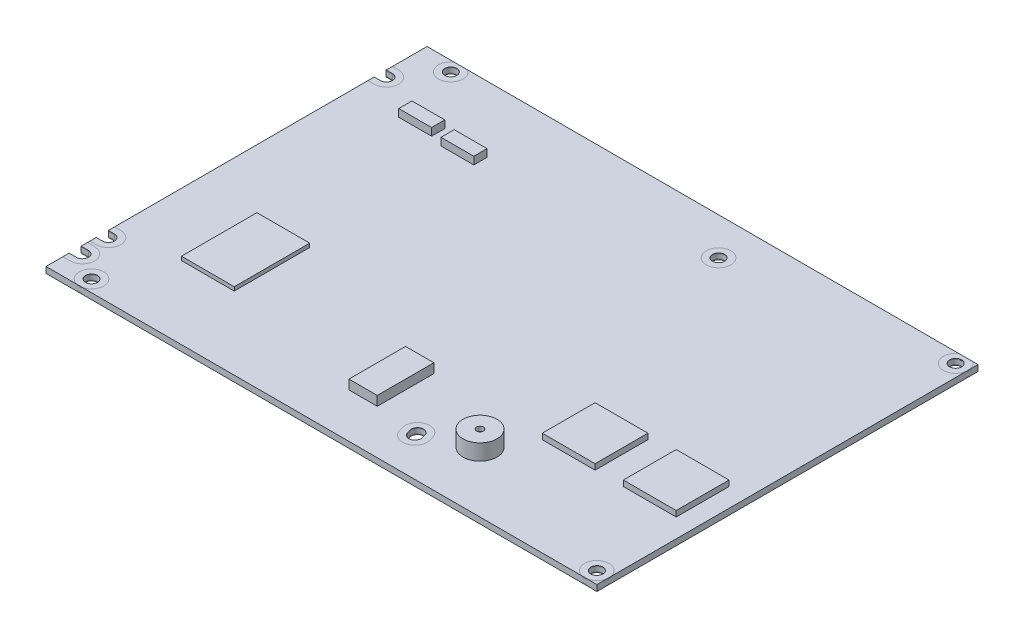
SolidWorks part; units mm, degrees
ref_plane "Alzado" through (0, 0, 0) normal (0, 0, 1) x (1, 0, 0)
ref_plane "Planta" through (0, 0, 0) normal (0, 1, 0) x (1, 0, 0)
ref_plane "Vista lateral" through (0, 0, 0) normal (1, 0, 0) x (0, 0, -1)
sketch "Croquis1" plane through (0, 0, 0) normal (0, 1, 0) x (1, 0, 0)
  line L0 (0, -14.02) -> (0, -84.48)
  line L1 (0, 0) -> (146.04, 0)
  line L2 (0, 0) -> (0, -10.82)
  line L3 (0, -101) -> (146.04, -101)
  line L4 (146.04, 0) -> (146.04, -101)
  line L5 (1.64, -10.82) -> (0, -10.82)
  line L6 (1.93, -91.68) -> (0, -91.68)
  line L7 (1.64, -14.02) -> (0, -14.02)
  line L8 (88.899, -89.4526) -> (89.169, -90.4026)
  line L9 (0, -94.88) -> (1.93, -94.88)
  line L10 (1.64, -84.48) -> (0, -84.48)
  line L11 (0, -94.88) -> (0, -101)
  line L12 (0, -87.68) -> (1.64, -87.68)
  line L13 (0, -87.68) -> (0, -91.68)
  line L14 (85.821, -90.3274) -> (86.091, -91.2774)
  circle A0 centre (8.99, -2.7) radius 1.6
  arc A1 (1.64, -14.02) -> (1.64, -10.82) centre (1.64, -12.42) ccw
  circle A2 centre (87.15, -9.88) radius 1.6
  circle A3 centre (142.8, -2.68) radius 1.6
  arc A4 (1.64, -87.68) -> (1.64, -84.48) centre (1.64, -86.08) ccw
  arc A5 (1.93, -94.88) -> (1.93, -91.68) centre (1.93, -93.28) ccw
  circle A6 centre (8.89, -97.82) radius 1.6
  circle A7 centre (142.8, -97.8) radius 1.6
  arc A8 (88.899, -89.4526) -> (85.821, -90.3274) centre (87.36, -89.89) ccw
  arc A9 (86.091, -91.2774) -> (89.169, -90.4026) centre (87.63, -90.84) ccw
  dimension "D3" = 3.2
  dimension "D6" = 3.2
  dimension "D10" = 3.2
  dimension "D13" = 3.2
  dimension "D16" = 3.2
  dimension "D17" = 3.2
  dimension "D22" = 3.2
  dimension "D25" = 3.2
  dimension "D28" = 3.2
  dimension "D29" = 3.2
  dimension "D1" = 146.04
  dimension "D2" = 101
  dimension "D4" = 8.99
  dimension "D5" = 2.7
  dimension "D7" = 1.64
  dimension "D8" = 12.42
  dimension "D9" = 3.2
  dimension "D11" = 87.15
  dimension "D12" = 9.88
  dimension "D14" = 2.68
  dimension "D15" = 142.8
  dimension "D18" = 1.93
  dimension "D19" = 1.64
  dimension "D20" = 86.08
  dimension "D21" = 93.28
  dimension "D23" = 8.89
  dimension "D24" = 97.82
  dimension "D26" = 142.8
  dimension "D27" = 97.8
  dimension "D30" = 87.36
  dimension "D31" = 87.63
  dimension "D32" = 89.89
  dimension "D33" = 90.84
extrude "Extruir1" add sketch "Croquis1" along normal blind 1.6
sketch "Croquis2" plane through (0, 1.6, 0) normal (0, 1, 0) x (1, 0, 0)
  line L0 (1.64, -9.17) -> (-2.3258, -9.17)
  line L1 (-2.3258, -9.17) -> (-2.3258, -15.67)
  line L2 (-2.3258, -15.67) -> (1.64, -15.67)
  line L3 (1.64, -82.83) -> (-3.1843, -82.83)
  line L4 (-3.1843, -82.83) -> (-3.1843, -89.33)
  line L5 (-3.1843, -89.33) -> (1.64, -89.33)
  line L6 (1.93, -90.03) -> (-3.1843, -90.03)
  line L7 (-3.1843, -90.03) -> (-3.1843, -96.53)
  line L8 (-3.1843, -96.53) -> (1.93, -96.53)
  line L9 (90.4862, -89.0015) -> (90.7562, -89.9515)
  line L10 (84.2338, -90.7785) -> (84.5038, -91.7285)
  circle A0 centre (8.99, -2.7) radius 3.25
  arc A1 (1.64, -15.67) -> (1.64, -9.17) centre (1.64, -12.42) ccw
  arc A2 (1.64, -89.33) -> (1.64, -82.83) centre (1.64, -86.08) ccw
  arc A3 (1.93, -96.53) -> (1.93, -90.03) centre (1.93, -93.28) ccw
  circle A4 centre (8.89, -97.82) radius 3.25
  circle A5 centre (87.15, -9.88) radius 3.25
  circle A6 centre (142.8, -2.68) radius 3.25
  circle A7 centre (142.8, -97.8) radius 3.25
  arc A8 (90.4862, -89.0015) -> (84.2338, -90.7785) centre (87.36, -89.89) ccw
  arc A9 (84.5038, -91.7285) -> (90.7562, -89.9515) centre (87.63, -90.84) ccw
  dimension "D1" = 6.5
  dimension "D2" = 6.5
  dimension "D3" = 6.5
  dimension "D4" = 6.5
  dimension "D5" = 6.5
  dimension "D6" = 6.5
  dimension "D7" = 6.5
  dimension "D8" = 6.5
  dimension "D9" = 6.5
  dimension "D10" = 6.5
extrude "Cortar-Extruir1" cut sketch "Croquis2" against normal blind 0.2
ref_plane "Plano1" through (0, 0.8, 0) normal (0, 1, 0) x (-1, 0, 0)
mirror "Simetría1" about plane through (0, 0.8, 0) normal (0, 1, 0) of "Cortar-Extruir1"
sketch "Croquis3" plane through (0, 1.4, 0) normal (0, 1, 0) x (1, 0, 0)
  line L0 (85.821, -90.3274) -> (86.091, -91.2774) construction
  line L1 (8.2191, -101) -> (9.5609, -101)
  line L2 (8.2191, -101) -> (9.5609, -101)
  line L3 (89.169, -90.4026) -> (88.899, -89.4526) construction
  line L4 (84.2338, -90.7785) -> (84.5038, -91.7285)
  line L5 (90.7562, -89.9515) -> (90.4862, -89.0015)
  line L6 (0, -90.03) -> (0, -91.68)
  line L7 (0, -91.68) -> (1.93, -91.68)
  line L8 (1.93, -94.88) -> (0, -94.88)
  line L9 (0, -94.88) -> (0, -96.53)
  line L10 (0, -96.53) -> (1.93, -96.53)
  line L11 (1.93, -90.03) -> (0, -90.03)
  line L12 (0, -90.03) -> (0, -91.68)
  line L13 (0, -91.68) -> (1.93, -91.68)
  line L14 (1.93, -94.88) -> (0, -94.88)
  line L15 (0, -94.88) -> (0, -96.53)
  line L16 (0, -96.53) -> (1.93, -96.53)
  line L17 (1.93, -90.03) -> (0, -90.03)
  line L18 (84.2338, -90.7785) -> (84.5038, -91.7285)
  line L19 (90.7562, -89.9515) -> (90.4862, -89.0015)
  line L20 (0, -82.83) -> (0, -84.48)
  line L21 (0, -84.48) -> (1.64, -84.48)
  line L22 (1.64, -87.68) -> (0, -87.68)
  line L23 (0, -87.68) -> (0, -89.33)
  line L24 (0, -89.33) -> (1.64, -89.33)
  line L25 (1.64, -82.83) -> (0, -82.83)
  line L26 (0, -82.83) -> (0, -84.48)
  line L27 (0, -84.48) -> (1.64, -84.48)
  line L28 (1.64, -87.68) -> (0, -87.68)
  line L29 (0, -87.68) -> (0, -89.33)
  line L30 (0, -89.33) -> (1.64, -89.33)
  line L31 (1.64, -82.83) -> (0, -82.83)
  line L32 (85.821, -90.3274) -> (86.091, -91.2774)
  line L33 (89.169, -90.4026) -> (88.899, -89.4526)
  line L35 (10.799, 0) -> (7.181, 0)
  line L36 (142.2321, -101) -> (143.3679, -101)
  line L37 (146.04, -98.0548) -> (146.04, -97.5452)
  line L38 (142.2321, -101) -> (143.3679, -101)
  line L39 (146.04, -98.0548) -> (146.04, -97.5452)
  line L40 (10.799, 0) -> (7.181, 0)
  line L42 (146.04, -2.9348) -> (146.04, -2.4252)
  line L43 (144.6385, 0) -> (140.9615, 0)
  line L44 (0, -9.17) -> (0, -10.82)
  line L45 (0, -10.82) -> (1.64, -10.82)
  line L46 (1.64, -14.02) -> (0, -14.02)
  line L47 (0, -14.02) -> (0, -15.67)
  line L48 (0, -15.67) -> (1.64, -15.67)
  line L49 (1.64, -9.17) -> (0, -9.17)
  line L50 (0, -9.17) -> (0, -10.82)
  line L51 (0, -10.82) -> (1.64, -10.82)
  line L52 (1.64, -14.02) -> (0, -14.02)
  line L53 (0, -14.02) -> (0, -15.67)
  line L54 (0, -15.67) -> (1.64, -15.67)
  line L55 (1.64, -9.17) -> (0, -9.17)
  line L56 (146.04, -2.9348) -> (146.04, -2.4252)
  line L57 (144.6385, 0) -> (140.9615, 0)
  circle A0 centre (8.89, -97.82) radius 1.6
  arc A1 (9.5609, -101) -> (8.2191, -101) centre (8.89, -97.82) ccw
  arc A2 (1.93, -94.88) -> (1.93, -91.68) centre (1.93, -93.28) ccw
  arc A3 (1.93, -96.53) -> (1.93, -90.03) centre (1.93, -93.28) ccw
  arc A4 (1.93, -94.88) -> (1.93, -91.68) centre (1.93, -93.28) ccw
  arc A5 (1.93, -96.53) -> (1.93, -90.03) centre (1.93, -93.28) ccw
  arc A6 (9.5609, -101) -> (8.2191, -101) centre (8.89, -97.82) ccw
  arc A7 (86.091, -91.2774) -> (89.169, -90.4026) centre (87.63, -90.84) ccw construction
  arc A8 (1.64, -87.68) -> (1.64, -84.48) centre (1.64, -86.08) ccw
  arc A9 (1.64, -89.33) -> (1.64, -82.83) centre (1.64, -86.08) ccw
  arc A10 (1.64, -87.68) -> (1.64, -84.48) centre (1.64, -86.08) ccw
  arc A11 (1.64, -89.33) -> (1.64, -82.83) centre (1.64, -86.08) ccw
  arc A12 (88.899, -89.4526) -> (85.821, -90.3274) centre (87.36, -89.89) ccw construction
  arc A13 (90.4862, -89.0015) -> (84.2338, -90.7785) centre (87.36, -89.89) ccw
  arc A14 (84.5038, -91.7285) -> (90.7562, -89.9515) centre (87.63, -90.84) ccw
  arc A15 (90.4862, -89.0015) -> (84.2338, -90.7785) centre (87.36, -89.89) ccw
  arc A16 (84.5038, -91.7285) -> (90.7562, -89.9515) centre (87.63, -90.84) ccw
  arc A17 (86.091, -91.2774) -> (89.169, -90.4026) centre (87.63, -90.84) ccw
  arc A18 (88.899, -89.4526) -> (85.821, -90.3274) centre (87.36, -89.89) ccw
  circle A19 centre (142.8, -97.8) radius 1.6
  circle A20 centre (8.99, -2.7) radius 1.6
  arc A21 (143.3679, -101) -> (146.04, -98.0548) centre (142.8, -97.8) ccw
  arc A22 (146.04, -97.5452) -> (142.2321, -101) centre (142.8, -97.8) ccw
  arc A23 (143.3679, -101) -> (146.04, -98.0548) centre (142.8, -97.8) ccw
  arc A24 (146.04, -97.5452) -> (142.2321, -101) centre (142.8, -97.8) ccw
  arc A25 (7.181, 0) -> (10.799, 0) centre (8.99, -2.7) ccw
  arc A26 (1.64, -14.02) -> (1.64, -10.82) centre (1.64, -12.42) ccw
  arc A27 (1.64, -15.67) -> (1.64, -9.17) centre (1.64, -12.42) ccw
  arc A28 (1.64, -14.02) -> (1.64, -10.82) centre (1.64, -12.42) ccw
  arc A29 (1.64, -15.67) -> (1.64, -9.17) centre (1.64, -12.42) ccw
  arc A30 (7.181, 0) -> (10.799, 0) centre (8.99, -2.7) ccw
  circle A31 centre (87.15, -9.88) radius 1.6
  circle A32 centre (87.15, -9.88) radius 3.25
  circle A33 centre (87.15, -9.88) radius 3.25
  circle A34 centre (142.8, -2.68) radius 1.6062
  arc A36 (146.04, -2.4252) -> (144.6385, 0) centre (142.8, -2.68) ccw
  arc A37 (140.9615, 0) -> (146.04, -2.9348) centre (142.8, -2.68) ccw
  arc A38 (146.04, -2.4252) -> (144.6385, 0) centre (142.8, -2.68) ccw
  arc A39 (140.9615, 0) -> (146.04, -2.9348) centre (142.8, -2.68) ccw
  dimension "D1" = 0
  dimension "D2" = 0
  dimension "D3" = 0
  dimension "D4" = 0
  dimension "D5" = 0
  dimension "D6" = 0
  dimension "D7" = 0
  dimension "D8" = 0
  dimension "D9" = 0
extrude "Extruir2" add sketch "Croquis3" along normal blind 0.2 separate body
mirror "Simetría2" about plane through (0, 0.8, 0) normal (0, 1, 0) of bodies 104 106 105 110 109 108 107 112 111
sketch "Croquis4" plane through (0, 1.6, 0) normal (0, 1, 0) x (1, 0, 0)
  line L0 (0, -15.67) -> (0, -82.83) construction
  line L1 (16.6, -61.7) -> (30.6, -61.7)
  line L2 (16.6, -61.7) -> (16.6, -81.7)
  line L3 (16.6, -81.7) -> (30.6, -81.7)
  line L4 (30.6, -61.7) -> (30.6, -81.7)
  line L5 (9.5609, -101) -> (142.2321, -101) construction
  dimension "D1" = 14
  dimension "D2" = 16.6
  dimension "D3" = 19.3
  dimension "D4" = 20
extrude "Extruir3" add sketch "Croquis4" along normal blind 1 separate body
sketch "Croquis5" plane through (0, 1.6, 0) normal (0, 1, 0) x (1, 0, 0)
  line L0 (146.04, -97.5452) -> (146.04, -2.9348) construction
  line L1 (105.54, -61) -> (119.54, -61)
  line L2 (105.54, -61) -> (105.54, -75)
  line L3 (105.54, -75) -> (119.54, -75)
  line L4 (119.54, -61) -> (119.54, -75)
  line L5 (127.04, -61) -> (141.04, -61)
  line L6 (127.04, -61) -> (127.04, -75)
  line L7 (127.04, -75) -> (141.04, -75)
  line L8 (141.04, -61) -> (141.04, -75)
  line L9 (9.5609, -101) -> (142.2321, -101) construction
  dimension "D1" = 5
  dimension "D2" = 14
  dimension "D3" = 14
  dimension "D4" = 14
  dimension "D5" = 7.5
  dimension "D6" = 26
extrude "Extruir4" add sketch "Croquis5" along normal blind 1.5 separate body
sketch "Croquis6" plane through (0, 1.6, 0) normal (0, 1, 0) x (1, 0, 0)
  line L0 (9.5609, -101) -> (142.2321, -101) construction
  line L1 (68.5, -74.2) -> (76, -74.2)
  line L2 (68.5, -74.2) -> (68.5, -89.2)
  line L3 (68.5, -89.2) -> (76, -89.2)
  line L4 (76, -74.2) -> (76, -89.2)
  line L5 (0, -15.67) -> (0, -82.83) construction
  point P4 (75.8965, -101)
  dimension "D1" = 7.5
  dimension "D2" = 15
  dimension "D3" = 26.8
  dimension "D4" = 76
extrude "Extruir5" add sketch "Croquis6" along normal blind 2.5 separate body
sketch "Croquis7" plane through (0, 0, 0) normal (0, -1, 0) x (1, 0, 0)
  line L0 (9.5609, 101) -> (142.2321, 101) construction
  line L1 (17.46, 62.99) -> (57.62, 62.99) construction
  line L2 (37.54, 62.99) -> (37.54, 71.9293) construction
  line L3 (0, 15.67) -> (0, 82.83) construction
  circle A0 centre (17.46, 62.99) radius 1
  circle A1 centre (57.62, 62.99) radius 1
  dimension "D1" = 2
  dimension "D2" = 2
  dimension "D3" = 40.16
  dimension "D4" = 38.01
  dimension "D5" = 37.54
extrude "Cortar-Extruir2" cut sketch "Croquis7" against normal blind 0.2
sketch "Croquis8" plane through (0, 1.6, 0) normal (0, 1, 0) x (1, 0, 0)
  line L0 (0, 0) -> (0, -9.17) construction
  line L1 (24.7, -17.5) -> (33.4, -17.5)
  line L2 (24.7, -17.5) -> (24.7, -21)
  line L3 (24.7, -21) -> (33.4, -21)
  line L4 (33.4, -17.5) -> (33.4, -21)
  line L5 (12.5, -16.5) -> (21.2, -16.5)
  line L6 (12.5, -16.5) -> (12.5, -20)
  line L7 (12.5, -20) -> (21.2, -20)
  line L8 (21.2, -16.5) -> (21.2, -20)
  line L9 (7.181, 0) -> (0, 0) construction
  line L10 (140.9615, 0) -> (10.799, 0) construction
  point P8 (0, -4.585)
  point P11 (3.5905, 0)
  dimension "D1" = 8.7
  dimension "D2" = 8.7
  dimension "D3" = 3.5
  dimension "D4" = 3.5
  dimension "D5" = 12.5
  dimension "D6" = 3.5
  dimension "D7" = 16.5
  dimension "D8" = 17.5
extrude "Extruir6" add sketch "Croquis8" along normal blind 2 separate body
sketch "Croquis9" plane through (0, 1.6, 0) normal (0, 1, 0) x (1, 0, 0)
  line L0 (146.04, -97.5452) -> (146.04, -2.9348) construction
  line L1 (9.5609, -101) -> (142.2321, -101) construction
  circle A0 centre (99.04, -85) radius 4.5
  dimension "D1" = 9
  dimension "D2" = 47
  dimension "D3" = 16
extrude "Extruir7" add sketch "Croquis9" along normal blind 4.2 separate body
sketch "Croquis10" plane through (0, 5.8, 0) normal (0, 1, 0) x (1, 0, 0)
  circle A0 centre (99.04, -85) radius 0.9153
extrude "Cortar-Extruir3" cut sketch "Croquis10" against normal blind 1.2
